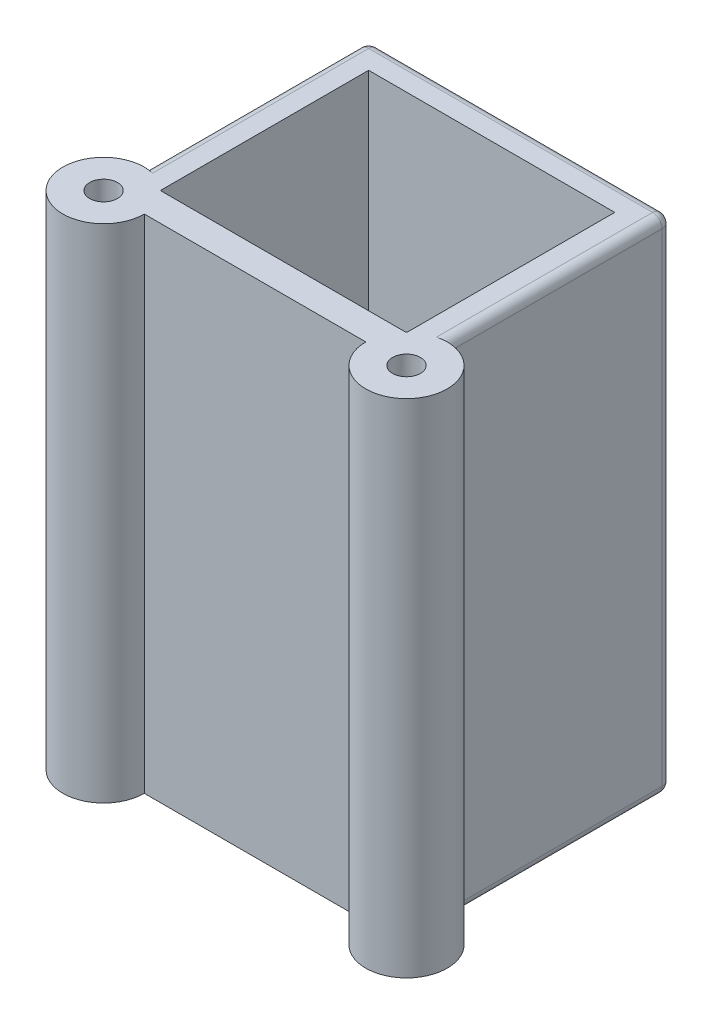
SolidWorks part; units mm, degrees
ref_plane "Front Plane" through (0, 0, 0) normal (0, 0, 1) x (1, 0, 0)
ref_plane "Top Plane" through (0, 0, 0) normal (0, 1, 0) x (1, 0, 0)
ref_plane "Right Plane" through (0, 0, 0) normal (1, 0, 0) x (0, 0, -1)
sketch "Sketch1" plane through (0, 0, 0) normal (0, 1, 0) x (1, 0, 0)
  line L1 (-32.7923, 16.6192) -> (-0.7923, 16.6192)
  line L2 (-32.7923, 16.6192) -> (-32.7923, -11.3808)
  line L3 (-32.7923, -11.3808) -> (-0.7923, -11.3808)
  line L4 (-0.7923, 16.6192) -> (-0.7923, -11.3808)
  dimension "D1" = 28
  dimension "D2" = 32
extrude "Boss-Extrude1" add sketch "Sketch1" along normal blind 53
sketch "Sketch2" plane through (0, 53, 0) normal (0, 1, 0) x (1, 0, 0)
  line L0 (-32.7923, 16.6192) -> (-32.7923, -11.3808) construction
  line L1 (-29.7923, -8.3808) -> (-3.7923, -8.3808)
  line L2 (-29.7923, -8.3808) -> (-29.7923, 13.6192)
  line L3 (-29.7923, 13.6192) -> (-3.7923, 13.6192)
  line L4 (-3.7923, -8.3808) -> (-3.7923, 13.6192)
  line L5 (-0.7923, 16.6192) -> (-32.7923, 16.6192) construction
  line L6 (-0.7923, -11.3808) -> (-0.7923, 16.6192) construction
  line L7 (-32.7923, -11.3808) -> (-0.7923, -11.3808) construction
  dimension "D1" = 3
  dimension "D2" = 3
  dimension "D3" = 3
  dimension "D4" = 3
extrude "Cut-Extrude1" cut sketch "Sketch2" against normal blind 56
sketch "Sketch9" plane through (0, 53, 0) normal (0, 1, 0) x (1, 0, 0)
  circle A0 centre (-32.7923, -11.3808) radius 4.3
extrude "Boss-Extrude5" add sketch "Sketch9" against normal blind 53
sketch "Sketch10" plane through (0, 53, 0) normal (0, 1, 0) x (1, 0, 0)
  line L0 (-29.7923, 13.6192) -> (-29.7923, -8.3002) construction
  line L1 (-29.7117, -8.3808) -> (-3.7923, -8.3808) construction
  circle A0 centre (-32.7923, -11.3808) radius 1.47
  dimension "D1" = 3
  dimension "D2" = 3
extrude "Cut-Extrude5" cut sketch "Sketch10" against normal blind 53
sketch "Sketch11" plane through (0, 53, 0) normal (0, 1, 0) x (1, 0, 0)
  circle A0 centre (-0.7923, -11.3808) radius 4.3
extrude "Boss-Extrude6" add sketch "Sketch11" against normal blind 53
sketch "Sketch12" plane through (0, 0, -13.6192) normal (0, 0, 1) x (1, 0, 0)
  line L0 (-29.7923, 0) -> (-29.7923, 53) construction
  line L1 (-3.7923, 0) -> (-29.7923, 0)
  line L2 (-3.7923, 0) -> (-3.7923, 3)
  line L3 (-3.7923, 3) -> (-29.7923, 3)
  line L4 (-29.7923, 0) -> (-29.7923, 3)
  dimension "D1" = 3
extrude "Boss-Extrude7" add sketch "Sketch12" along normal blind 10
sketch "Sketch13" plane through (0, 53, 0) normal (0, 1, 0) x (1, 0, 0)
  circle A0 centre (-0.7923, -11.3808) radius 1.47
extrude "Cut-Extrude6" cut sketch "Sketch13" against normal blind 53
fillet "Fillet1" radius 1 8 edges at (-0.7923, 53, -4.7692) (-0.7923, 0, -4.7692) (-32.7923, 53, -4.7692) (-16.7923, 53, -16.6192) (-0.7923, 26.5, -16.6192) (-16.7923, 0, -16.6192) (-32.7923, 0, -4.7692) (-32.7923, 26.5, -16.6192)
